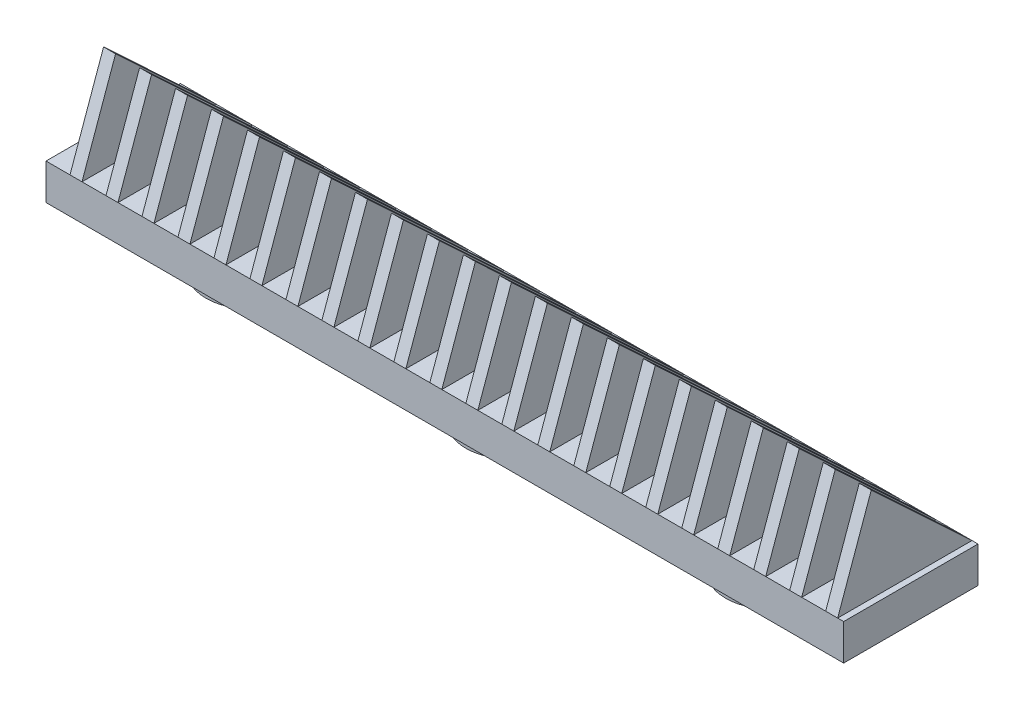
SolidWorks part; units mm, degrees
ref_plane "Front Plane" through (0, 0, 0) normal (0, 0, 1) x (1, 0, 0)
ref_plane "Top Plane" through (0, 0, 0) normal (0, 1, 0) x (1, 0, 0)
ref_plane "Right Plane" through (0, 0, 0) normal (1, 0, 0) x (0, 0, -1)
sketch "Sketch1" plane through (0, 0, 0) normal (0, 1, 0) x (1, 0, 0)
  line L1 (0, 0) -> (-211.1375, 0)
  line L2 (0, 0) -> (0, 35.56)
  line L3 (0, 35.56) -> (-211.1375, 35.56)
  line L4 (-211.1375, 0) -> (-211.1375, 35.56)
  dimension "D1" = 211.1375
extrude "Boss-Extrude1" add sketch "Sketch1" along normal blind 9.525
sketch "Sketch2" plane through (0, 9.525, 0) normal (0, 1, 0) x (1, 0, 0)
  line L0 (-211.1375, 0) -> (0, 0) construction
  line L1 (-211.1375, 35.56) -> (-207.8355, 35.56)
  line L2 (-211.1375, 35.56) -> (-211.1375, 0)
  line L3 (-211.1375, 0) -> (-207.8355, 0)
  line L4 (-207.8355, 35.56) -> (-207.8355, 0)
  dimension "D1" = 3.302
ref_plane "Plane1" through (0, 34.417, 0) normal (0, 1, 0) x (1, 0, 0)
sketch "Sketch5" plane through (0, 34.417, 0) normal (0, 1, 0) x (1, 0, 0)
  line L2 (-213.741, 8.89) -> (-207.8355, 8.89)
  line L3 (-207.8355, 35.56) -> (-207.8355, 0) construction
sketch "Sketch6" plane through (0, 0, 0) normal (0, -1, 0) x (-1, 0, 0)
  line L5 (0, 0) -> (0, 35.56) construction
  line L6 (211.1375, 35.56) -> (211.1375, 0) construction
  circle A0 centre (105.5687, 17.78) radius 12.192
  circle A1 centre (36.7982, 17.78) radius 12.192
  circle A2 centre (174.3392, 17.78) radius 12.192
  dimension "D1" = 36.7982
  dimension "D2" = 24.384
  dimension "D3" = 68.7705
  dimension "D4" = 24.384
  dimension "D5" = 24.384
  dimension "D6" = 36.7983
  dimension "D7" = 68.7705
extrude "Boss-Extrude4" add sketch "Sketch6" along normal blind 6.35
sketch3d "3DSketch1"
  line L0 (-207.8355, 9.525, -35.56) -> (-207.8355, 9.525, 0)
  line L1 (-207.8355, 9.525, 0) -> (-207.8355, 34.417, -8.89)
  line L2 (-207.8355, 34.417, -8.89) -> (-207.8355, 9.525, -35.56)
ref_plane "Plane2" through (-204.7875, 0, 0) normal (-1, 0, 0) x (0, 0, 1)
sketch "Sketch9" plane through (-204.7875, 0, 0) normal (-1, 0, 0) x (0, 0, 1)
  line L0 (-35.56, 9.525) -> (0, 9.525)
  line L1 (0, 9.525) -> (-8.89, 34.417)
  line L2 (-8.89, 34.417) -> (-35.56, 9.525)
extrude "Boss-Extrude5" add sketch "Sketch9" against normal blind 3.175
pattern_linear "LPattern1" count 22 spacing 9.525 along (1, 0, 0) of "Boss-Extrude5"
